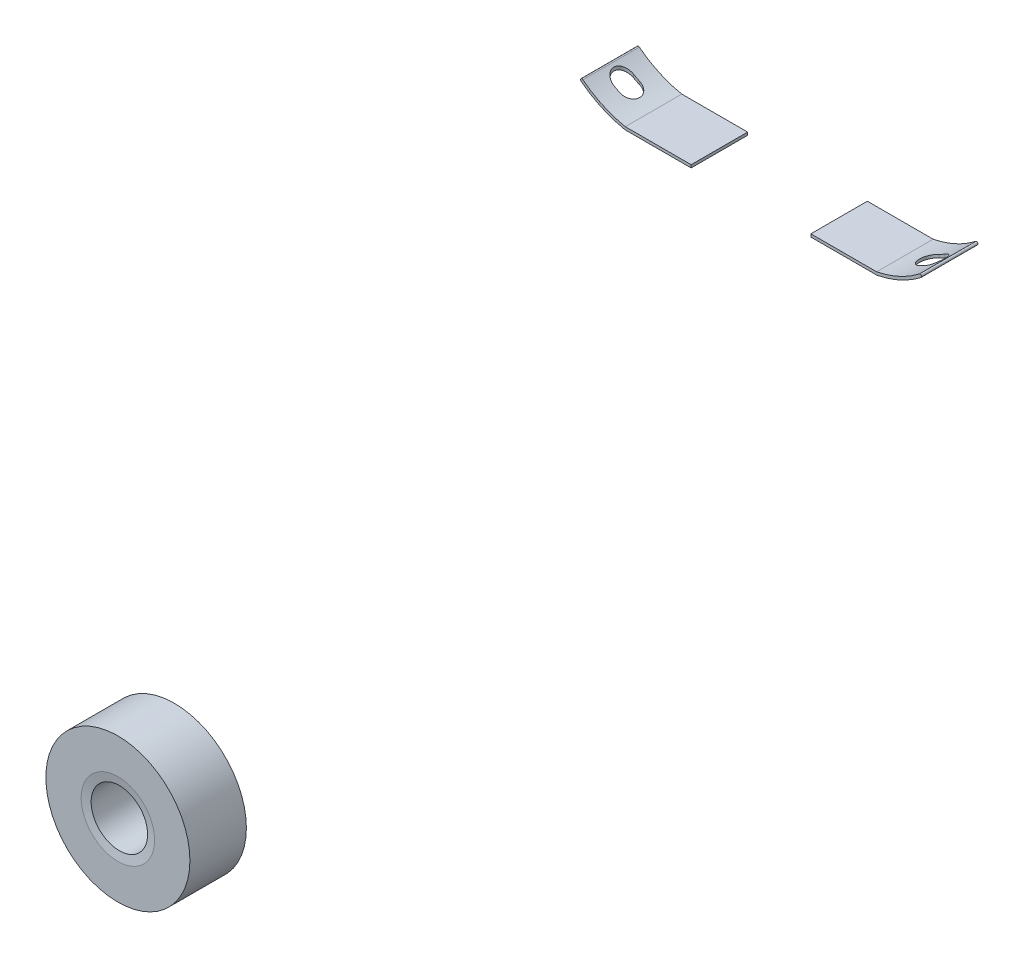
SolidWorks part; units mm, degrees
ref_plane "Front Plane" through (0, 0, 0) normal (0, 0, 1) x (1, 0, 0)
ref_plane "Top Plane" through (0, 0, 0) normal (0, 1, 0) x (1, 0, 0)
ref_plane "Right Plane" through (0, 0, 0) normal (1, 0, 0) x (0, 0, -1)
sketch "Sketch1" plane through (0, 0, 0) normal (0, 0, 1) x (1, 0, 0)
  line L0 (0, 7.6004) -> (0, 9.4242) construction
  line L1 (2.1192, 7.6951) -> (4.4585, 7.6951)
  line L2 (2.1192, 7.7951) -> (4.4488, 7.7951)
  line L3 (2.1192, 7.6951) -> (2.1192, 7.7951)
  line L4 (-2.1192, 7.6951) -> (-2.1192, 7.7951)
  line L5 (-2.1192, 7.7951) -> (-4.4488, 7.7951)
  line L6 (-2.1192, 7.6951) -> (-4.4585, 7.6951)
  arc A0 (4.4585, 7.6951) -> (6.0181, 8.405) centre (3.7607, 11.296) ccw
  arc A1 (4.4488, 7.7951) -> (5.9566, 8.4839) centre (3.7607, 11.296) ccw
  arc A2 (5.9566, 8.4839) -> (6.0181, 8.405) centre (5.9873, 8.4444) cw
  arc A3 (-5.9566, 8.4839) -> (-6.0181, 8.405) centre (-5.9873, 8.4444) ccw
  arc A4 (-4.4488, 7.7951) -> (-5.9566, 8.4839) centre (-3.7607, 11.296) cw
  arc A5 (-4.4585, 7.6951) -> (-6.0181, 8.405) centre (-3.7607, 11.296) cw
extrude "Boss-Extrude1" add sketch "Sketch1" along normal blind 2
sketch "Sketch2" plane through (0, 7.6951, 0) normal (0, -1, 0) x (1, 0, 0)
  line L0 (5.3022, 0.6386) -> (5.5128, 0.6386)
  line L1 (5.3022, 1.3386) -> (5.5128, 1.3386)
  line L3 (-5.3022, 1.3386) -> (-5.5128, 1.3386)
  line L4 (-5.3022, 0.6386) -> (-5.5128, 0.6386)
  arc A0 (5.3022, 1.3386) -> (5.3022, 0.6386) centre (5.3022, 0.9886) ccw
  arc A1 (5.5128, 0.6386) -> (5.5128, 1.3386) centre (5.5128, 0.9886) ccw
  arc A2 (-5.5128, 0.6386) -> (-5.5128, 1.3386) centre (-5.5128, 0.9886) cw
  arc A3 (-5.3022, 1.3386) -> (-5.3022, 0.6386) centre (-5.3022, 0.9886) cw
  dimension "D1" = 0.7
extrude "Cut-Extrude1" cut sketch "Sketch2" against normal blind 2
ref_plane "Plane1" through (0, 0, 24.4161) normal (0, 0, 1) x (1, 0, 0)
sketch "Sketch3" plane through (0, 0, 24.4161) normal (0, 0, 1) x (1, 0, 0)
  circle A0 centre (0, 0) radius 2.55 construction
  circle A1 centre (0, 0) radius 2.55
  circle A2 centre (0, 0) radius 1 construction
  circle A3 centre (0, 0) radius 1
extrude "Boss-Extrude2" add sketch "Sketch3" against normal blind 2 separate body
chamfer "Chamfer1" distance 0.3 angle 10 1 edges at (1, 0, 24.4161)
